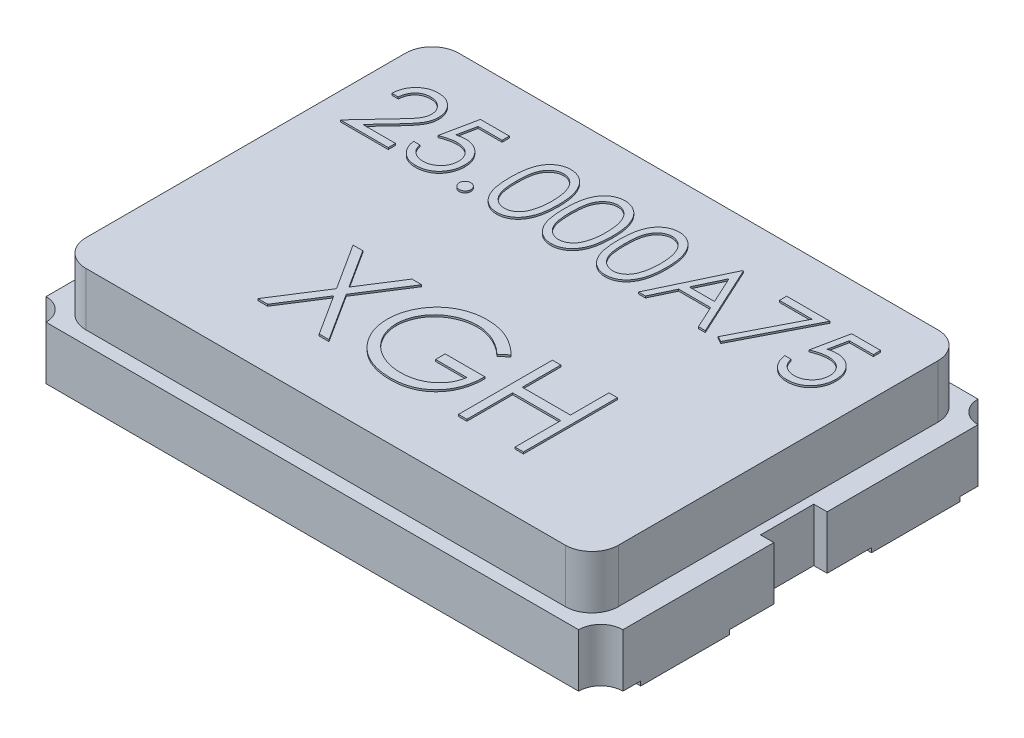
SolidWorks part; units mm, degrees
ref_plane "Plano frontal" through (0, 0, 0) normal (0, 0, 1) x (1, 0, 0)
ref_plane "Plano superior" through (0, 0, 0) normal (0, 1, 0) x (1, 0, 0)
ref_plane "Plano direito" through (0, 0, 0) normal (1, 0, 0) x (0, 0, -1)
sketch "Sketch1" plane through (0, 0, 0) normal (0, 1, 0) x (1, 0, 0)
  line L0 (-3.25, 2) -> (-3.25, 0.3)
  line L5 (-3.25, 0.3) -> (-3.1, 0.3)
  line L7 (-3.25, -0.3) -> (-3.1, -0.3)
  line L8 (-3.1, 0.3) -> (-3.1, -0.3)
  line L9 (3.25, 0.3) -> (3.1, 0.3)
  line L11 (3.25, -0.3) -> (3.1, -0.3)
  line L12 (3.1, 0.3) -> (3.1, -0.3)
  line L13 (-3.25, -0.3) -> (-3.25, -2)
  line L14 (-3, -2.25) -> (3, -2.25)
  line L15 (3.25, -2) -> (3.25, -0.3)
  line L16 (3.25, 0.3) -> (3.25, 2)
  line L17 (3, 2.25) -> (-3, 2.25)
  arc A0 (-3.25, 2) -> (-3, 2.25) centre (-3.25, 2.25) ccw
  arc A1 (-3, -2.25) -> (-3.25, -2) centre (-3.25, -2.25) ccw
  arc A2 (3.25, -2) -> (3, -2.25) centre (3.25, -2.25) ccw
  arc A3 (3, 2.25) -> (3.25, 2) centre (3.25, 2.25) ccw
  dimension "D5" = 0.25
  dimension "D6" = 0.25
  dimension "D7" = 0.25
  dimension "D8" = 0.25
  dimension "D2" = 1.7
  dimension "D3" = 1.7
  dimension "D4" = 1.7
  dimension "D9" = 0.6
  dimension "D10" = 0.3
  dimension "D11" = 0.15
  dimension "D12" = 0.15
  dimension "D13" = 0.6
  dimension "D14" = 6
  dimension "D15" = 6
  dimension "D16" = 3
  dimension "D17" = 0.25
  dimension "D18" = 0.25
  dimension "D19" = 0.25
  dimension "D20" = 0.25
extrude "Extrude1" add sketch "Sketch1" along normal blind 0.6
sketch "Sketch2" plane through (0, 0.6, 0) normal (0, 1, 0) x (1, 0, 0)
  line L1 (-2.7, 2.1) -> (2.7, 2.1)
  line L2 (-3, 1.8) -> (-3, -1.8)
  line L3 (-2.7, -2.1) -> (2.7, -2.1)
  line L4 (3, 1.8) -> (3, -1.8)
  arc A0 (3.25, -2) -> (3, -2.25) centre (3.25, -2.25) ccw construction
  arc A1 (-2.7, 2.1) -> (-3, 1.8) centre (-2.7, 1.8) ccw
  arc A2 (2.7, 2.1) -> (3, 1.8) centre (2.7, 1.8) cw
  arc A3 (2.7, -2.1) -> (3, -1.8) centre (2.7, -1.8) ccw
  arc A4 (-3, -1.8) -> (-2.7, -2.1) centre (-2.7, -1.8) ccw
  point P10 (-3, 2.1)
  point P13 (3, 2.1)
  point P16 (3.0128, -2.1709)
  point P19 (-2.8, -3.1)
  dimension "D4" = 0.3
  dimension "D1" = 3
  dimension "D2" = 6
  dimension "D3" = 2.1
  dimension "D5" = 2.1
extrude "Extrude2" add sketch "Sketch2" along normal blind 0.6
sketch "Sketch3" plane through (0, 0, 0) normal (0, -1, 0) x (1, 0, 0)
  line L1 (-3.25, 0.3) -> (-3.25, 2) construction
  line L2 (-3.25, 1.8) -> (-2.25, 1.8)
  line L3 (-3.25, 1.8) -> (-3.25, 0.8)
  line L4 (-3.25, 0.8) -> (-2.25, 0.8)
  line L6 (-2.25, 1.8) -> (-2.25, 0.8)
  line L7 (-3.25, -2) -> (-3.25, -0.3) construction
  line L8 (-3.25, -1.8) -> (-2.25, -1.8)
  line L9 (-3.25, -1.8) -> (-3.25, -0.8)
  line L10 (-3.25, -0.8) -> (-2.25, -0.8)
  line L11 (-2.25, -1.8) -> (-2.25, -0.8)
  line L12 (3.25, 2) -> (3.25, 0.3) construction
  line L13 (3.25, 1.8) -> (2.25, 1.8)
  line L14 (3.25, 1.8) -> (3.25, 0.8)
  line L15 (3.25, 0.8) -> (2.25, 0.8)
  line L16 (2.25, 1.8) -> (2.25, 0.8)
  line L17 (3.25, -0.3) -> (3.25, -2) construction
  line L18 (3.25, -0.8) -> (2.25, -0.8)
  line L19 (3.25, -0.8) -> (3.25, -1.8)
  line L20 (3.25, -1.8) -> (2.25, -1.8)
  line L21 (2.25, -0.8) -> (2.25, -1.8)
  dimension "D1" = 1
  dimension "D2" = 1
  dimension "D3" = 1
  dimension "D4" = 1
  dimension "D5" = 1
  dimension "D6" = 1
  dimension "D7" = 1
  dimension "D8" = 1
  dimension "D9" = 0.8
  dimension "D10" = 0.8
  dimension "D11" = 0.8
  dimension "D12" = 0.8
extrude "Extrude3" add sketch "Sketch3" along normal blind 0.05
sketch "Sketch4" plane through (0, 1.2, 0) normal (0, 1, 0) x (1, 0, 0)
  text T0 "25.000A75" font "Century Gothic" height in points 3
extrude "Extrude4" add sketch "Sketch4" along normal blind 0.02
sketch "Sketch5" plane through (0, 1.2, 0) normal (0, 1, 0) x (1, 0, 0)
  text T0 "XGH" font "Century Gothic" height in points 4
extrude "Extrude5" add sketch "Sketch5" along normal blind 0.02
